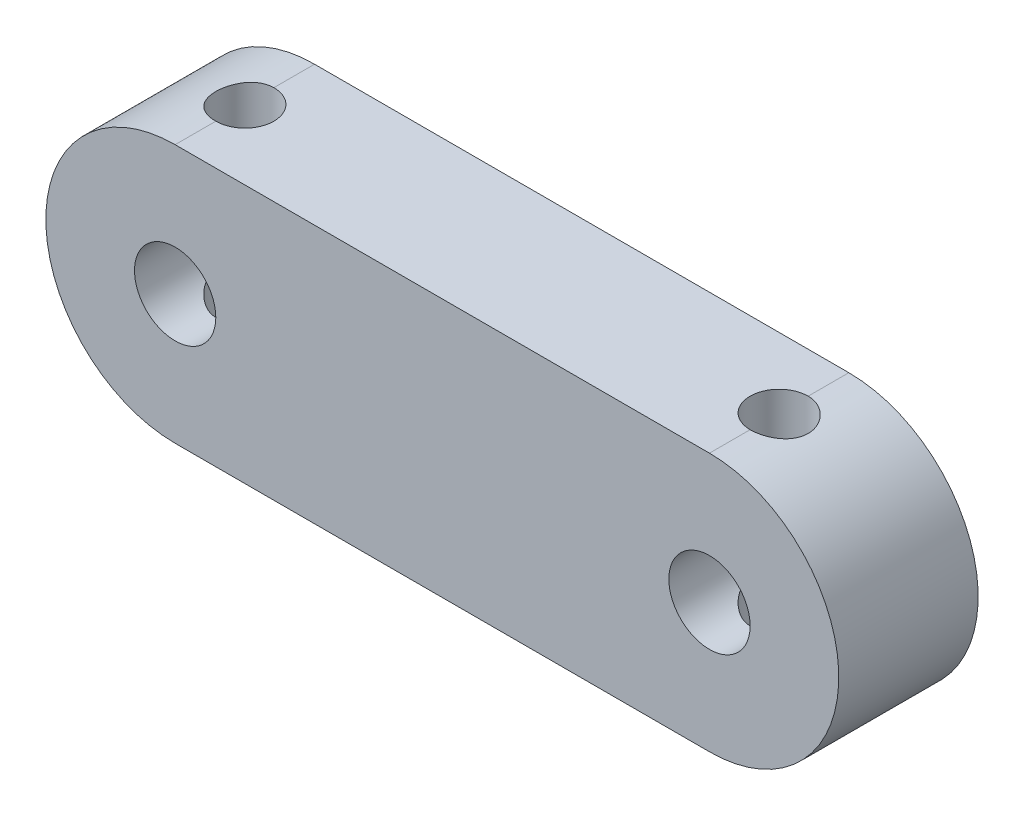
SolidWorks part; units mm, degrees
material "AISI 304"
ref_plane "Front Plane" through (0, 0, 0) normal (0, 0, 1) x (1, 0, 0)
ref_plane "Top Plane" through (0, 0, 0) normal (0, 1, 0) x (1, 0, 0)
ref_plane "Right Plane" through (0, 0, 0) normal (1, 0, 0) x (0, 0, -1)
sketch "Sketch1" plane through (0, 0, 0) normal (0, 0, 1) x (1, 0, 0)
  line L0 (-4.4654, 0) -> (18.5346, 0) construction
  line L1 (-4.4654, 5.5665) -> (18.5346, 5.5665)
  line L2 (-4.4654, -5.5665) -> (18.5346, -5.5665)
  arc A0 (-4.4654, 5.5665) -> (-4.4654, -5.5665) centre (-4.4654, 0) ccw
  arc A1 (18.5346, -5.5665) -> (18.5346, 5.5665) centre (18.5346, 0) ccw
  circle A2 centre (-4.4654, 0) radius 1.75
  circle A3 centre (18.5346, 0) radius 1.75
  point P3 (7.0346, 0)
  dimension "D1" = 23
extrude "Boss-Extrude1" add sketch "Sketch1" along normal blind 6
sketch "Sketch2" plane through (0, 0, 0) normal (0, 1, 0) x (1, 0, 0)
  line L0 (18.5346, -6) -> (18.5346, 0) construction
  line L1 (-4.4654, -6) -> (-4.4654, 0) construction
  circle A0 centre (18.5346, -3) radius 1.25
  circle A1 centre (-4.4654, -3) radius 1.25
extrude "Cut-Extrude1" cut sketch "Sketch2" against normal through all both and the other way through all
